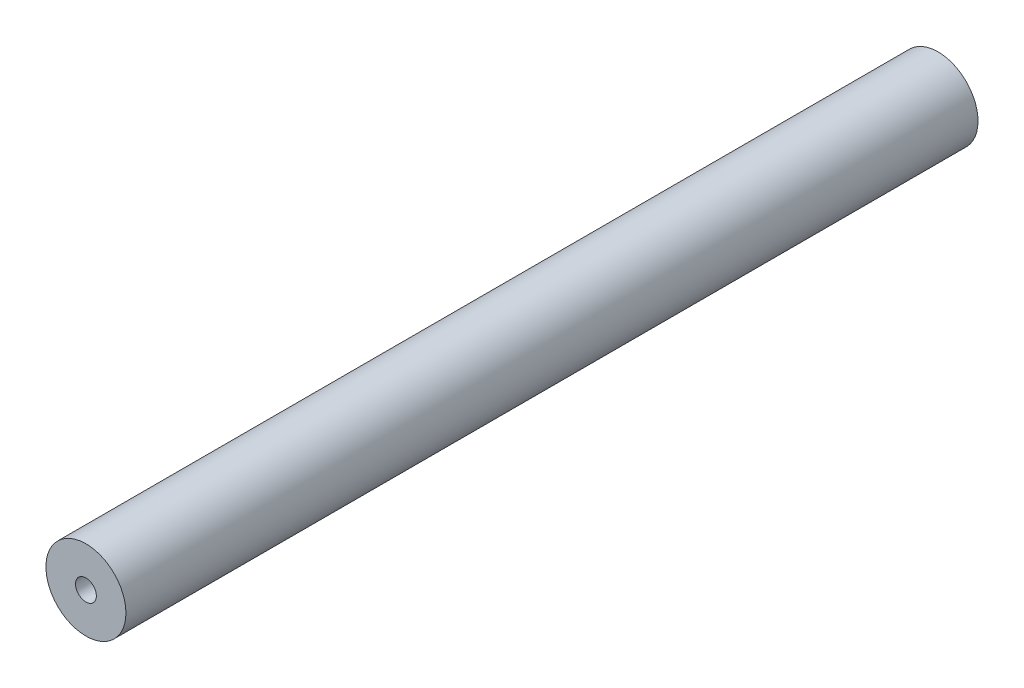
SolidWorks part; units mm, degrees
material "Cast Alloy Steel"
ref_plane "Front Plane" through (0, 0, 0) normal (0, 0, 1) x (1, 0, 0)
ref_plane "Top Plane" through (0, 0, 0) normal (0, 1, 0) x (1, 0, 0)
ref_plane "Right Plane" through (0, 0, 0) normal (1, 0, 0) x (0, 0, -1)
sketch "Sketch2" plane through (0, 0, 0) normal (0, 0, 1) x (1, 0, 0)
  circle A0 centre (0, 0) radius 115
  circle A1 centre (0, 0) radius 30
  dimension "D1" = 230
  dimension "D2" = 60
extrude "Boss-Extrude1" add sketch "Sketch2" along normal blind 2450
scale "Scale1" bodies to scale 101 scale about centroid uniform scaling yes scale factor 0.1
